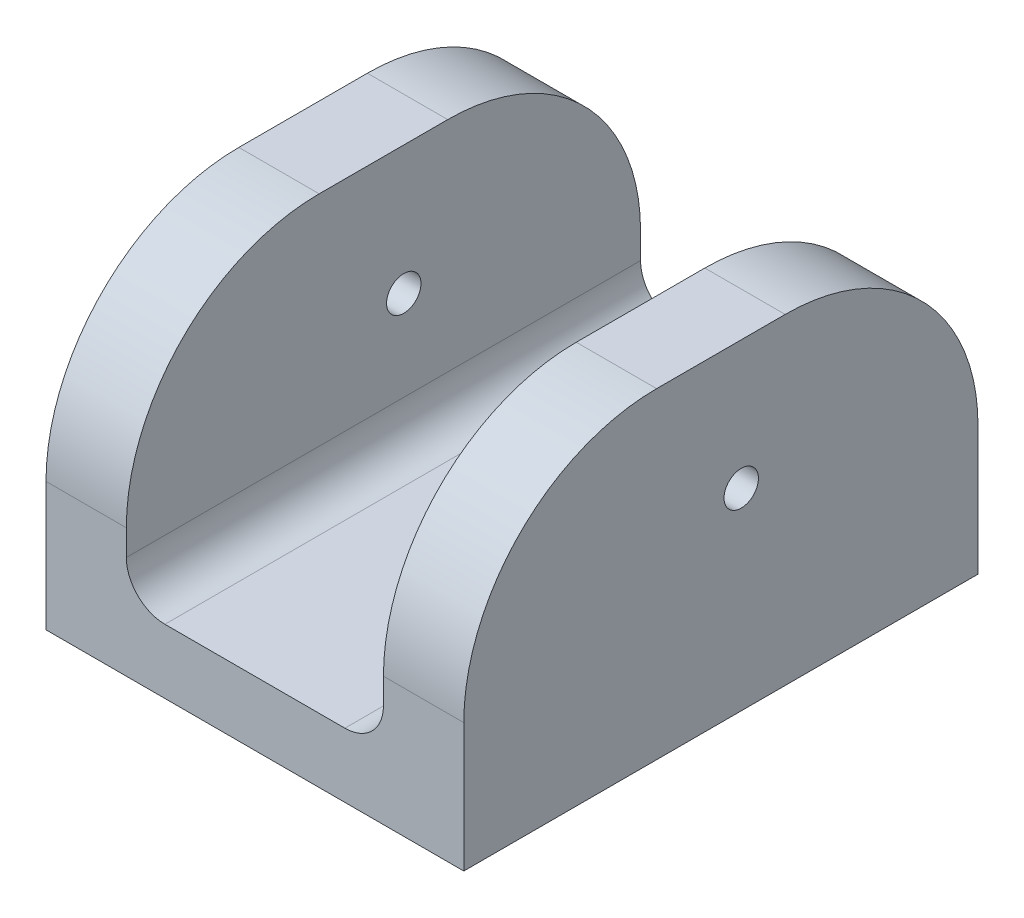
SolidWorks part; units mm, degrees
material "6061-T6 (SS)"
ref_plane "Front Plane" through (0, 0, 0) normal (0, 0, 1) x (1, 0, 0)
ref_plane "Top Plane" through (0, 0, 0) normal (0, 1, 0) x (1, 0, 0)
ref_plane "Right Plane" through (0, 0, 0) normal (1, 0, 0) x (0, 0, -1)
sketch "Sketch1" plane through (0, 0, 0) normal (0, 0, 1) x (1, 0, 0)
  line L0 (-20.6375, 0) -> (20.6375, 0)
  line L1 (20.6375, 0) -> (20.6375, 6.35)
  line L3 (20.6375, 6.35) -> (20.6375, 31.75)
  line L4 (20.6375, 31.75) -> (12.7, 31.75)
  line L5 (12.7, 31.75) -> (12.7, 6.35)
  line L6 (12.7, 6.35) -> (-12.7, 6.35)
  line L7 (0, 6.35) -> (0, 0) construction
  line L8 (-12.7, 31.75) -> (-12.7, 6.35)
  line L9 (-20.6375, 31.75) -> (-12.7, 31.75)
  line L10 (-20.6375, 6.35) -> (-20.6375, 31.75)
  line L12 (-20.6375, 0) -> (-20.6375, 6.35)
  point P4 (0, 0)
  dimension "D2" = 6.35
  dimension "D3" = 25.4
  dimension "D4" = 25.4
  dimension "D5" = 7.9375
extrude "Boss-Extrude1" add sketch "Sketch1" along normal blind 50.8
sketch "Sketch2" plane through (0, 0, 0) normal (0, 1, 0) x (1, 0, 0)
  line L0 (12.7, -25.4) -> (-12.7, -25.4) construction
  line L1 (12.7, -50.8) -> (-12.7, -50.8) construction
  line L2 (12.7, -50.8) -> (12.7, 0) construction
  line L3 (12.7, 0) -> (-12.7, 0) construction
  line L4 (-12.7, -50.8) -> (-12.7, 0) construction
  point P6 (0, -31.75)
  point P10 (0, -19.05)
  point P12 (0, -50.8)
  dimension "D1" = 19.05
fillet "Fillet1" radius 19.05 4 edges at (-16.6688, 31.75, 50.8) (16.6687, 31.75, 50.8) (-16.6688, 31.75, 0) (16.6687, 31.75, 0)
fillet "Fillet2" [suppressed] radius 2.54
fillet "Fillet3" radius 3.81 2 edges at (12.7, 6.35, 25.4) (-12.7, 6.35, 25.4)
sketch "Sketch21" plane through (0, 0, 0) normal (0, 1, 0) x (1, 0, 0)
  line L0 (20.6375, -31.75) -> (20.6375, -19.05) construction
  line L1 (20.6375, 0) -> (12.7, 0) construction
  line L2 (20.6375, 0) -> (20.6375, -7.9375) construction
  line L3 (20.6375, -7.9375) -> (12.7, -7.9375) construction
  line L4 (12.7, 0) -> (12.7, -7.9375) construction
  line L5 (-20.6375, 0) -> (-12.7, 0) construction
  line L6 (12.7, 0) -> (12.7, -50.8) construction
  line L7 (20.6375, -7.9375) -> (12.7, 0) construction
  line L8 (20.6375, 0) -> (12.7, -7.9375) construction
  line L9 (0, 0) -> (0, -50.8) construction
  line L10 (-20.6375, 0) -> (20.6375, 0) construction
  line L11 (-20.6375, -50.8) -> (20.6375, -50.8) construction
  line L12 (-20.6375, -25.4) -> (20.6375, -25.4) construction
  line L13 (-20.6375, -50.8) -> (-20.6375, 0) construction
  line L14 (20.6375, -50.8) -> (20.6375, 0) construction
  point P10 (16.6687, -3.9688)
  point P24 (-16.6687, -3.9688)
  point P26 (16.6687, -46.8312)
  point P27 (-16.6687, -46.8312)
hole_wizard "1/4-20 Tapped Hole1" positions "Sketch22" profile "Sketch23" tap size "1/4-20" standard "ANSI Inch"
sketch "Sketch22" plane through (0, 0, 0) normal (0, -1, 0) x (-1, 0, 0)
  point P0 (-16.6687, -3.9688)
  point P3 (16.6687, -3.9688)
  point P6 (16.6687, -46.8312)
  point P9 (-16.6687, -46.8312)
sketch "Sketch23" plane through (16.6687, 0, 3.9688) normal (1, 0, 0) x (0, 0, -1)
  line L0 (0, 0) -> (0, 20.5838)
  line L1 (0, 20.5838) -> (2.5527, 19.05)
  line L2 (2.5527, 19.05) -> (2.5527, 0)
  line L5 (2.5527, 0) -> (0, 0)
  line L10 (0, 20.5838) -> (-2.5527, 19.05) construction
  line L11 (0, -6.35) -> (0, 107.95) construction
  dimension "Tap Drill Dia." = 5.1054
  dimension "Tap Drill Depth" = 19.05
  dimension "Drill Angle" = 118
cosmetic thread "Hole Thread1" parameters "D1"=12.7, "D2"=6.35
cosmetic thread "Hole Thread2" parameters "D1"=12.7, "D2"=6.35
cosmetic thread "Hole Thread3" parameters "D1"=12.7, "D2"=6.35
cosmetic thread "Hole Thread4" parameters "D1"=12.7, "D2"=6.35
sketch "Sketch28" plane through (0, 0, 0) normal (1, 0, 0) x (0, 0, -1)
  line L0 (-184.15, 112.9665) -> (-23.3911, 19.05) construction
  line L1 (-50.8, 0) -> (0, 0) construction
  point P3 (0, 0)
  dimension "D1" = 186.182
  dimension "D2" = 19.05
hole_wizard "M3 Clearance Hole2" positions "Sketch29" profile "Sketch30" hole size "M3" standard "ANSI Metric" end condition through all
sketch "Sketch29" plane through (20.6375, 0, 0) normal (1, 0, 0) x (0, 0, -1)
  point P0 (-23.3911, 19.05)
sketch "Sketch30" plane through (20.6375, 19.05, 23.3911) normal (0, 1, 0) x (0, 0, -1)
  line L0 (0, 0) -> (0, 41.275)
  line L1 (0, 41.275) -> (1.7, 41.275)
  line L2 (1.7, 41.275) -> (1.7, 0)
  line L5 (1.7, 0) -> (0, 0)
  line L11 (0, -6.35) -> (0, 107.95) construction
  dimension "Thru Hole Dia." = 3.4
  dimension "Thru Hole Depth" = 41.275
equation "\"D1@Sketch28\"=7.33"
